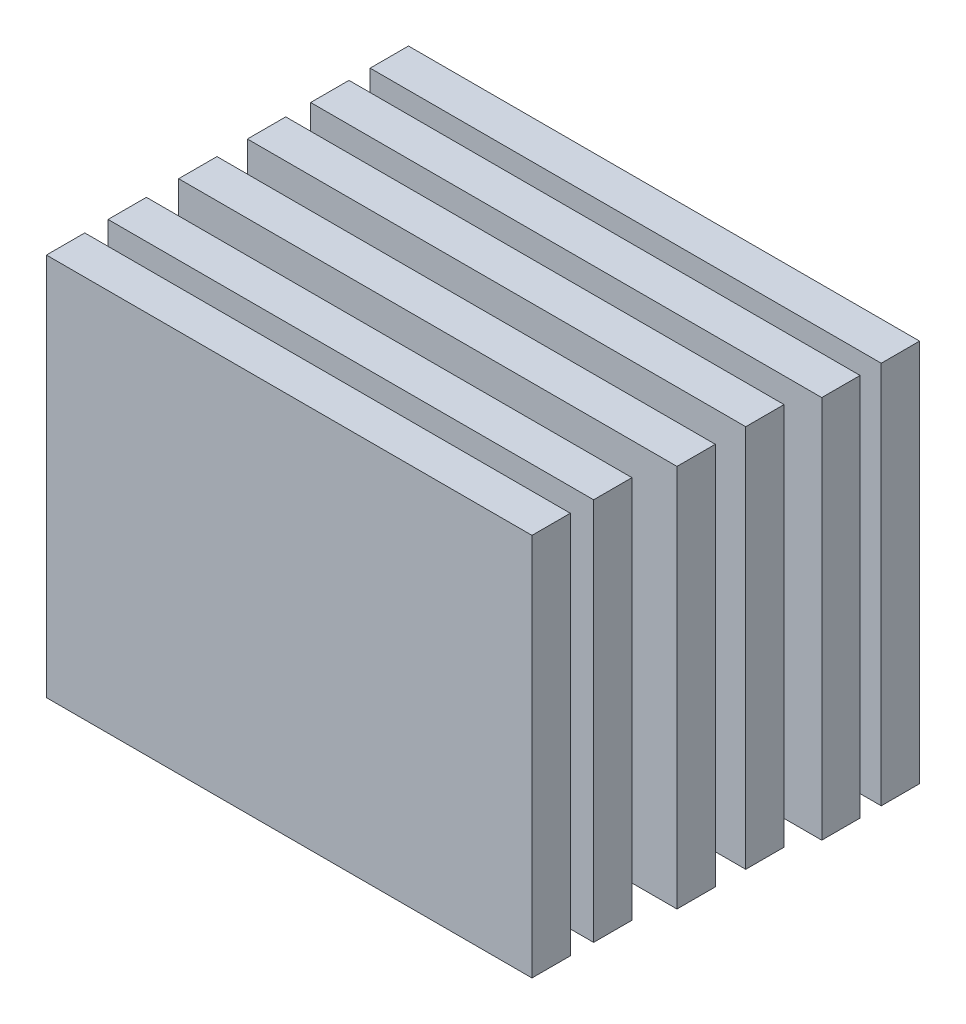
SolidWorks part; units mm, degrees
ref_plane "Front Plane" through (0, 0, 0) normal (0, 0, 1) x (1, 0, 0)
ref_plane "Top Plane" through (0, 0, 0) normal (0, 1, 0) x (1, 0, 0)
ref_plane "Right Plane" through (0, 0, 0) normal (1, 0, 0) x (0, 0, -1)
sketch "Sketch1" plane through (0, 0, 0) normal (0, 1, 0) x (1, 0, 0)
  line L1 (0, 0) -> (39, 0)
  line L2 (0, 0) -> (0, -3)
  line L3 (0, -3) -> (39, -3)
  line L4 (39, 0) -> (39, -3)
  line L5 (0, -5.5238) -> (38, -5.5238)
  line L6 (0, -5.5238) -> (0, -8.5238)
  line L7 (0, -8.5238) -> (38, -8.5238)
  line L8 (38, -5.5238) -> (38, -8.5238)
  line L9 (0, 2.381) -> (39, 2.381)
  line L10 (0, 2.381) -> (0, 5.381)
  line L11 (0, 5.381) -> (39, 5.381)
  line L12 (39, 2.381) -> (39, 5.381)
  line L13 (0, 7.3306) -> (40, 7.3306)
  line L14 (0, 7.3306) -> (0, 10.3306)
  line L15 (0, 10.3306) -> (40, 10.3306)
  line L16 (40, 7.3306) -> (40, 10.3306)
  line L17 (0, -10.3478) -> (38, -10.3478)
  line L18 (0, -10.3478) -> (0, -13.3478)
  line L19 (0, -13.3478) -> (38, -13.3478)
  line L20 (38, -10.3478) -> (38, -13.3478)
  line L21 (0, 11.9865) -> (40, 11.9865)
  line L22 (0, 11.9865) -> (0, 14.9865)
  line L23 (0, 14.9865) -> (40, 14.9865)
  line L24 (40, 11.9865) -> (40, 14.9865)
  dimension "D1" = 3
  dimension "D2" = 39
  dimension "D3" = 3
  dimension "D4" = 38
  dimension "D5" = 39
  dimension "D6" = 3
  dimension "D7" = 40
  dimension "D8" = 3
  dimension "D9" = 3
  dimension "D10" = 3
extrude "Boss-Extrude1" add sketch "Sketch1" along normal blind 30
